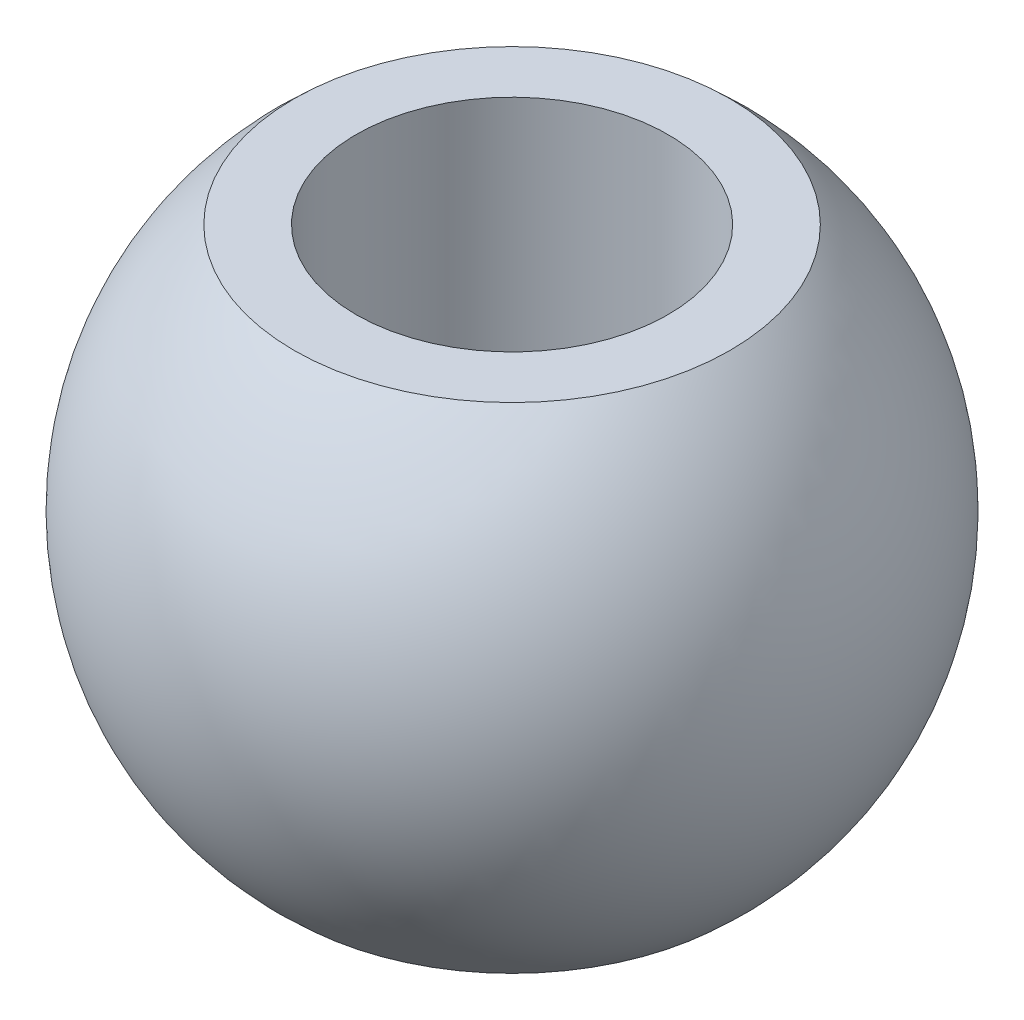
SolidWorks part; units mm, degrees
ref_plane "Front Plane" through (0, 0, 0) normal (0, 0, 1) x (1, 0, 0)
ref_plane "Top Plane" through (0, 0, 0) normal (0, 1, 0) x (1, 0, 0)
ref_plane "Right Plane" through (0, 0, 0) normal (1, 0, 0) x (0, 0, -1)
sketch "Sketch1" plane through (0, 0, 0) normal (0, 0, 1) x (1, 0, 0)
  line L0 (0, 2.3876) -> (0, -2.3876)
  arc A0 (0, 2.3876) -> (0, -2.3876) centre (0, 0) cw
revolve "Revolve1" add sketch "Sketch1" angle 360 about L0
ref_plane "Plane1" through (0, 1.7907, 0) normal (0, 1, 0) x (-1, 0, 0)
sketch "Sketch2" plane through (0, 1.7907, 0) normal (0, 1, 0) x (-1, 0, 0)
  circle A0 centre (0, 0) radius 2.3876
extrude "Extrude1" cut sketch "Sketch2" along normal through all
mirror "Mirror1" about plane through (0, 0, 0) normal (0, 1, 0) of "Extrude1"
sketch "Sketch3" plane through (0, 1.7907, 0) normal (0, 1, 0) x (-1, 0, 0)
  circle A0 centre (0, 0) radius 1.1303
extrude "Extrude2" cut sketch "Sketch3" against normal through all
